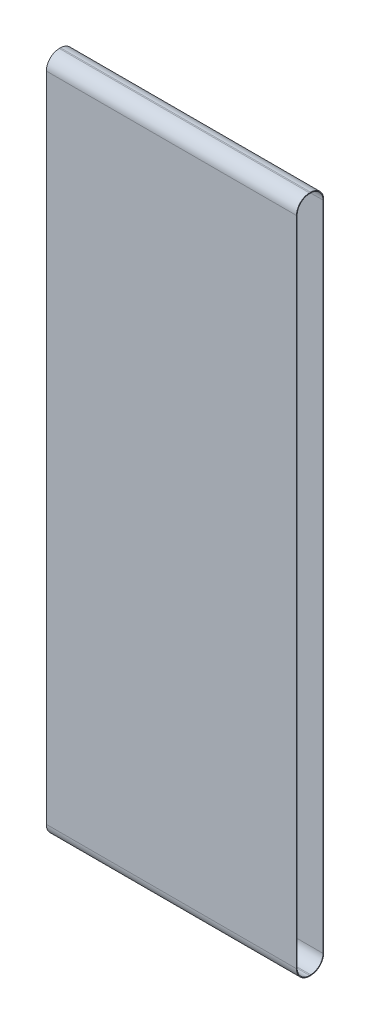
SolidWorks part; units mm, degrees
ref_plane "Front Plane" through (0, 0, 0) normal (0, 0, 1) x (1, 0, 0)
ref_plane "Top Plane" through (0, 0, 0) normal (0, 1, 0) x (1, 0, 0)
ref_plane "Right Plane" through (0, 0, 0) normal (1, 0, 0) x (0, 0, -1)
sketch "Sketch1" plane through (0, 0, 0) normal (0, 1, 0) x (1, 0, 0)
  line L1 (241.3, -26.289) -> (-241.3, -26.289)
  line L2 (241.3, -26.289) -> (241.3, 26.289)
  line L3 (241.3, 26.289) -> (-241.3, 26.289)
  line L4 (-241.3, -26.289) -> (-241.3, 26.289)
  line L5 (241.3, -26.289) -> (-241.3, 26.289) construction
  line L6 (241.3, 26.289) -> (-241.3, -26.289) construction
  point P0 (0, 0)
  dimension "D1" = 482.6
  dimension "D2" = 52.578
extrude "Boss-Extrude1" add sketch "Sketch1" along normal blind 1308.608
fillet "Fillet1" radius 25.1206 4 edges at (0, 1308.608, -26.289) (0, 1308.608, 26.289) (0, 0, -26.289) (0, 0, 26.289)
sketch "Sketch2" plane through (241.3, 0, 0) normal (1, 0, 0) x (0, 0, -1)
  line L0 (1.1684, 1308.608) -> (1.1684, 0) construction
  line L10 (24.9428, 25.1206) -> (24.9428, 1283.4874)
  line L11 (1.1684, 1307.2618) -> (-1.1684, 1307.2618)
  line L12 (-24.9428, 1283.4874) -> (-24.9428, 25.1206)
  line L13 (-1.1684, 1.3462) -> (1.1684, 1.3462)
  line L14 (24.9428, 25.1206) -> (24.9428, 1283.4874)
  line L15 (1.1684, 1307.2618) -> (-1.1684, 1307.2618)
  line L16 (-24.9428, 1283.4874) -> (-24.9428, 25.1206)
  line L17 (-1.1684, 1.3462) -> (1.1684, 1.3462)
  arc A8 (24.9428, 1283.4874) -> (1.1684, 1307.2618) centre (1.1684, 1283.4874) ccw
  arc A9 (-1.1684, 1307.2618) -> (-24.9428, 1283.4874) centre (-1.1684, 1283.4874) ccw
  arc A10 (-24.9428, 25.1206) -> (-1.1684, 1.3462) centre (-1.1684, 25.1206) ccw
  arc A11 (1.1684, 1.3462) -> (24.9428, 25.1206) centre (1.1684, 25.1206) ccw
  arc A12 (24.9428, 1283.4874) -> (1.1684, 1307.2618) centre (1.1684, 1283.4874) ccw
  arc A13 (-1.1684, 1307.2618) -> (-24.9428, 1283.4874) centre (-1.1684, 1283.4874) ccw
  arc A14 (-24.9428, 25.1206) -> (-1.1684, 1.3462) centre (-1.1684, 25.1206) ccw
  arc A15 (1.1684, 1.3462) -> (24.9428, 25.1206) centre (1.1684, 25.1206) ccw
  dimension "D1" = 1.3462
extrude "Cut-Extrude1" cut sketch "Sketch2" against normal through all
